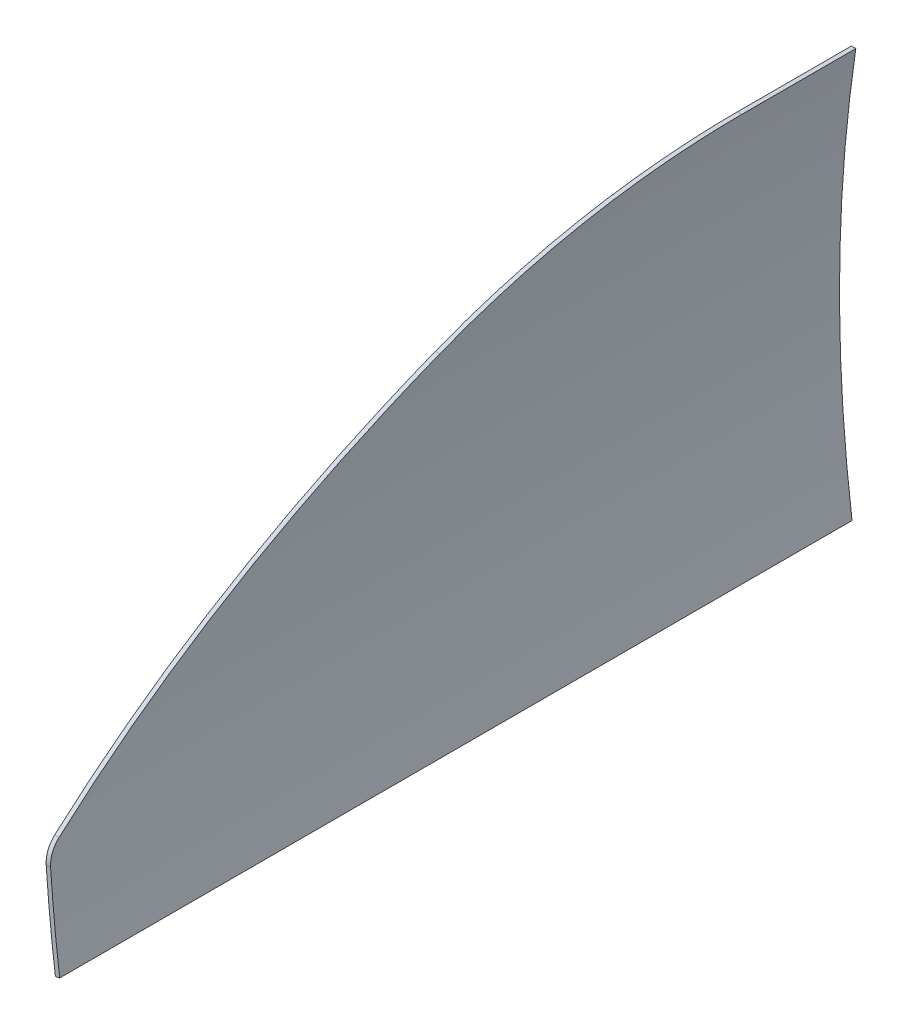
SolidWorks part; units mm, degrees
ref_plane "Front Plane" through (0, 0, 0) normal (0, 0, 1) x (1, 0, 0)
ref_plane "Top Plane" through (0, 0, 0) normal (0, 1, 0) x (1, 0, 0)
ref_plane "Right Plane" through (0, 0, 0) normal (1, 0, 0) x (0, 0, -1)
sketch "Sketch1" plane through (0, 0, 0) normal (0, 0, 1) x (1, 0, 0)
  arc A0 (0, 0) -> (0, 500) centre (1662.9127, 250) cw
  dimension "D2" = 1681.6
  dimension "D1" = 500
extrude "Extrude-Thin1" add sketch "Sketch1" along normal mid plane 1000 thin thin type mid plane wall 5
sketch "Sketch2" plane through (0, 0, 0) normal (1, 0, 0) x (0, 0, -1)
  line L6 (500, 499.6283) -> (370, 499.6283)
  line L7 (-500, 499.6283) -> (500, 499.6283) construction
  line L13 (-404, 30.1883) -> (500, 30.1883)
  line L14 (500, 30.1883) -> (500, 499.6283)
  line L15 (-404, 30.1883) -> (-404, 135.1883)
  arc A1 (370, 499.6283) -> (34.5992, 425.9246) centre (370, -300.3717) ccw
  arc A2 (34.5992, 425.9246) -> (-392.9914, 158.4117) centre (873.1013, -1389.8161) ccw
  arc A4 (-404, 135.1883) -> (-392.9914, 158.4117) centre (-374, 135.1883) cw
  point P5 (0, 0)
  point P17 (-398.8682, 125.4804)
  point P20 (-500, 279.0366)
  dimension "D1" = 130
  dimension "D2" = 904
  dimension "D7" = 800
  dimension "D8" = 2000
  dimension "D6" = 30
  dimension "D3" = 105
extrude "Cut-Extrude1" cut sketch "Sketch2" against normal mid plane 80 flip side to cut
sketch "Sketch3" plane through (0, 0, 404) normal (0, 0, 1) x (1, 0, 0)
  line L0 (-6.7806, 30.1883) -> (-1.8582, 31.1057)
  line L1 (-1.8582, 31.1057) -> (-1.7373, 30.1883)
  line L2 (-1.7373, 30.1883) -> (-6.7806, 30.1883)
  arc A0 (-12.2575, 135.1883) -> (-1.7373, 30.1883) centre (1662.9127, 250) ccw construction
  point P6 (-1.8582, 31.1057)
extrude "Cut-Extrude2" cut sketch "Sketch3" against normal through all
